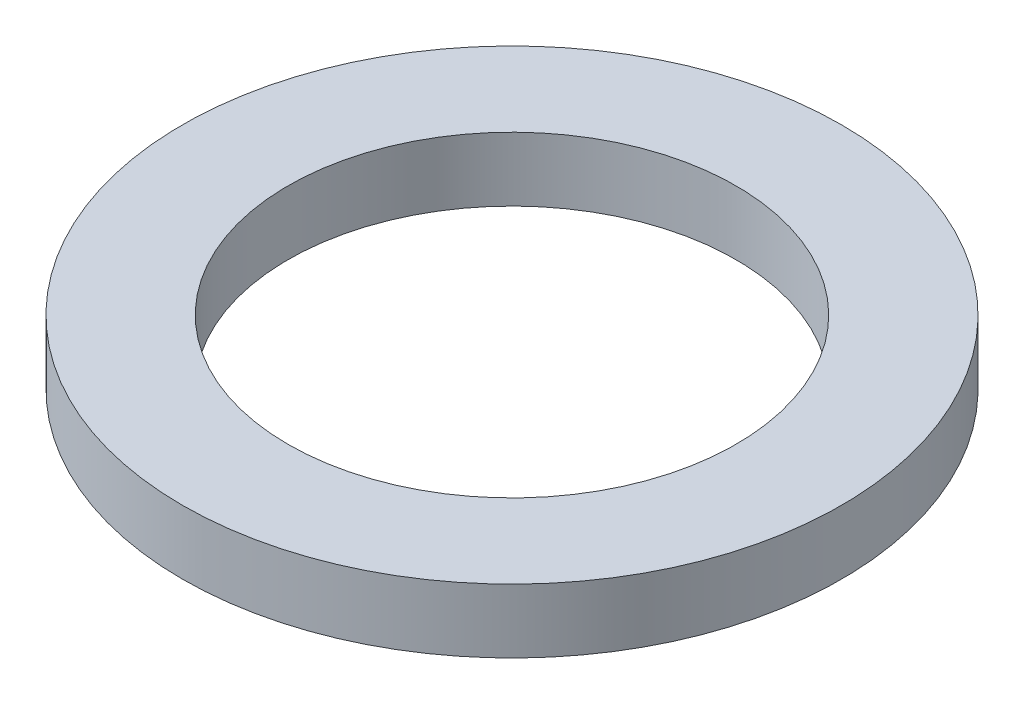
SolidWorks part; units mm, degrees
material "1.6523 (20NiCrMoS2-2)"
ref_plane "Front Plane" through (0, 0, 0) normal (0, 0, 1) x (1, 0, 0)
ref_plane "Top Plane" through (0, 0, 0) normal (0, 1, 0) x (1, 0, 0)
ref_plane "Right Plane" through (0, 0, 0) normal (1, 0, 0) x (0, 0, -1)
sketch "Sketch1" plane through (0, 0, 0) normal (0, 1, 0) x (1, 0, 0)
  circle A0 centre (0, 0) radius 10.3
  circle A1 centre (0, 0) radius 7
  dimension "D1" = 20.6
  dimension "D2" = 14
extrude "Boss-Extrude1" add sketch "Sketch1" along normal blind 2
